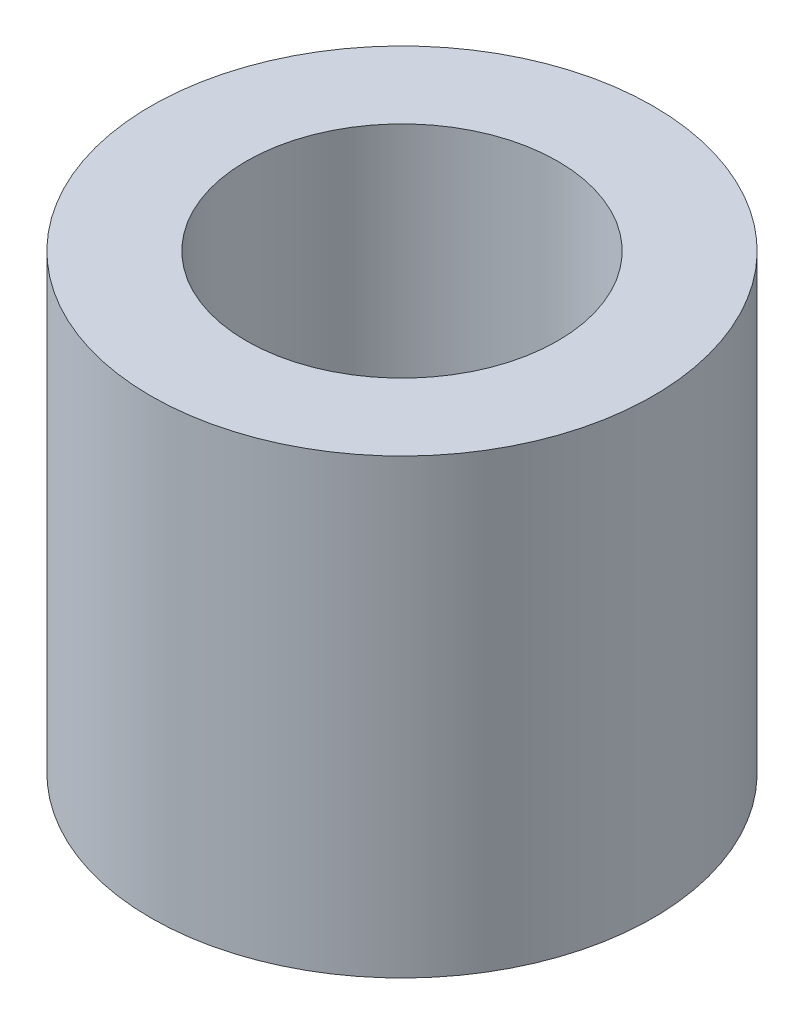
SolidWorks part; units mm, degrees
material "6061 合金"
ref_plane "前视基准面" through (0, 0, 0) normal (0, 0, 1) x (1, 0, 0)
ref_plane "上视基准面" through (0, 0, 0) normal (0, 1, 0) x (1, 0, 0)
ref_plane "右视基准面" through (0, 0, 0) normal (1, 0, 0) x (0, 0, -1)
sketch "草图1" plane through (0, 0, 0) normal (0, 1, 0) x (1, 0, 0)
  circle A0 centre (0, 0) radius 1.55
  circle A1 centre (0, 0) radius 2.5
  dimension "D1" = 5
  dimension "D2" = 3.1
extrude "凸台-拉伸1" add sketch "草图1" along normal blind 4.5
